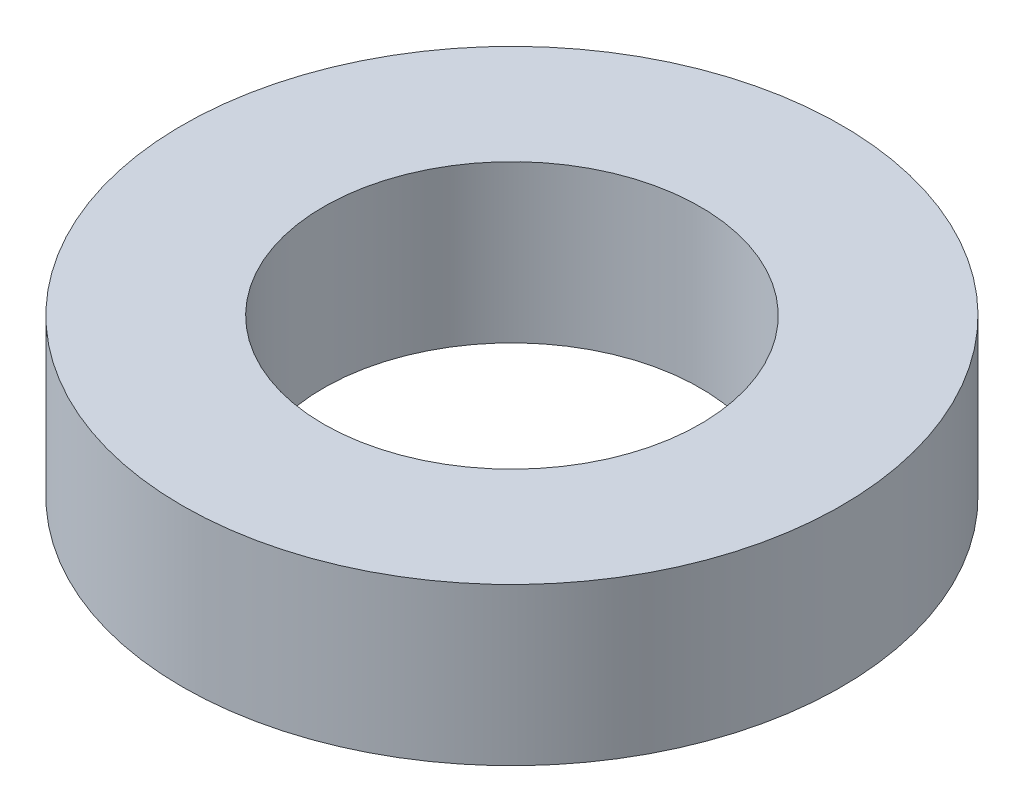
SolidWorks part; units mm, degrees
material "1023 Carbon Steel Sheet (SS)"
ref_plane "Front Plane" through (0, 0, 0) normal (0, 0, 1) x (1, 0, 0)
ref_plane "Top Plane" through (0, 0, 0) normal (0, 1, 0) x (1, 0, 0)
ref_plane "Right Plane" through (0, 0, 0) normal (1, 0, 0) x (0, 0, -1)
ref_axis "Axis1" through (0, 55, 0) along (0, -1, 0)
sketch "Sketch1" plane through (0, 0, 0) normal (0, 0, 1) x (1, 0, 0)
  line L0 (0, 55) -> (0, -55) construction
  line L1 (-10.5, -2.5) -> (-6, -2.5)
  line L2 (-10.5, -2.5) -> (-10.5, 2.5)
  line L3 (-10.5, 2.5) -> (-6, 2.5)
  line L4 (-6, -2.5) -> (-6, 2.5)
  line L5 (-10.5, -2.5) -> (-6, 2.5) construction
  line L6 (-10.5, 2.5) -> (-6, -2.5) construction
  line L7 (0, 0) -> (0, 24.718) construction
  point P0 (-8.25, 0)
  dimension "D1" = 12
  dimension "D2" = 21
  dimension "D3" = 5
revolve "Revolve1" add sketch "Sketch1" angle 360 about axis through (0, 55, 0) along (0, -1, 0)
